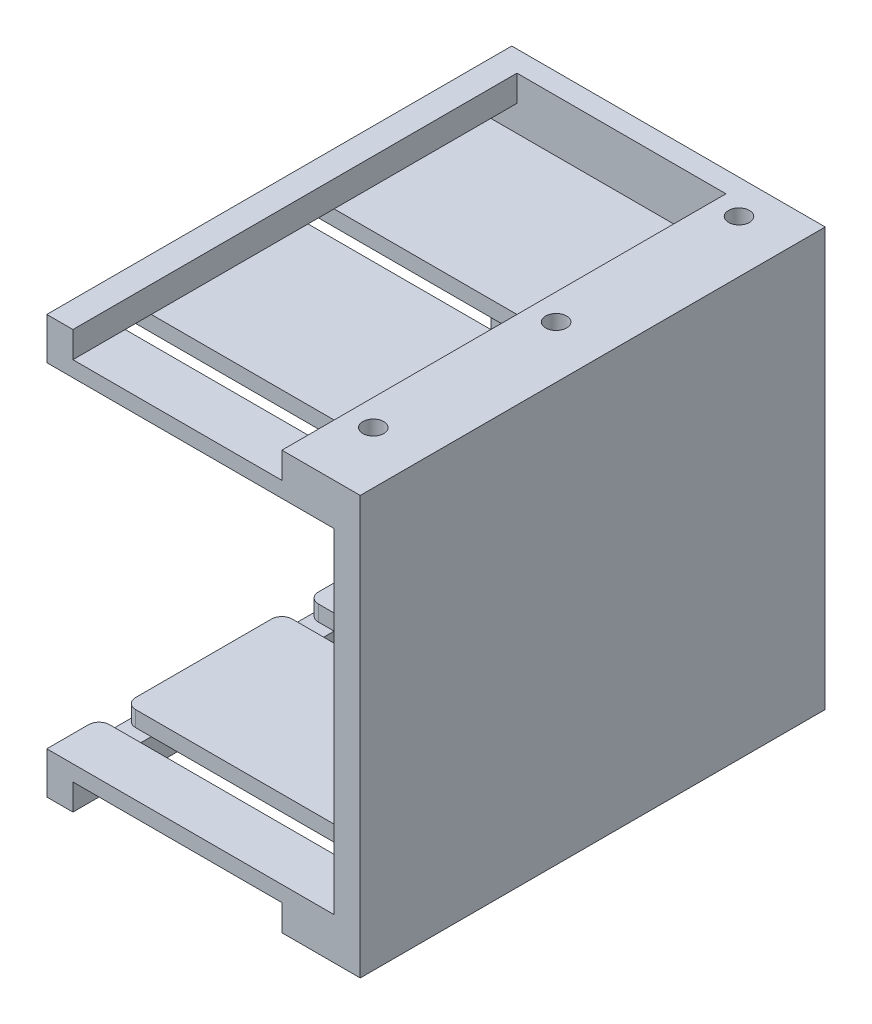
SolidWorks part; units mm, degrees
ref_plane "Front Plane" through (0, 0, 0) normal (1, 0, 0) x (0, 1, 0)
ref_plane "Top Plane" through (0, 0, 0) normal (0, 0, 1) x (0, 1, 0)
ref_plane "Right Plane" through (0, 0, 0) normal (0, 1, 0) x (-1, 0, 0)
sketch "Sketch1" plane through (0, 0, 0) normal (0, 0, 1) x (0, 1, 0)
  line L1 (0, 0) -> (-80, 0)
  line L2 (0, 0) -> (0, -60)
  line L3 (0, -60) -> (-80, -60)
  line L4 (-80, 0) -> (-80, -60)
  dimension "D1" = 80
  dimension "D2" = 60
extrude "Boss-Extrude1" add sketch "Sketch1" along normal blind 4
sketch "Sketch3" plane through (0, 0, 4) normal (0, 0, 1) x (1, 0, 0)
  line L0 (0, -40) -> (60, -40) construction
  line L1 (0, 0) -> (5, 0)
  line L2 (0, 0) -> (0, -5)
  line L3 (0, -5) -> (5, -5)
  line L4 (5, 0) -> (5, -5)
  line L5 (0, 0) -> (0, -80) construction
  line L6 (60, -80) -> (60, 0) construction
  line L7 (0, -75) -> (5, -75)
  line L8 (5, -80) -> (5, -75)
  line L9 (0, -80) -> (5, -80)
  line L10 (0, -80) -> (0, -75)
  line L16 (60, 0) -> (0, 0) construction
  line L17 (60, 0) -> (55, 0)
  line L18 (60, 0) -> (60, -80)
  line L19 (60, -80) -> (52.7053, -80)
  line L20 (55, -5) -> (55, -75)
  line L22 (55, -5) -> (45, -5)
  line L24 (55, 0) -> (45, 0)
  line L25 (45, -5) -> (45, 0)
  line L26 (52.7053, -80) -> (45, -80)
  line L28 (55, -75) -> (45, -75)
  line L29 (45, -80) -> (45, -75)
  dimension "D1" = 5
  dimension "D2" = 5
  dimension "D3" = 15
extrude "Boss-Extrude2" add sketch "Sketch3" along normal blind 85
sketch "Sketch9" plane through (55, 0, 0) normal (-1, 0, 0) x (0, -1, 0)
  line L0 (5, 89) -> (5, 4) construction
  line L1 (5, 9) -> (8, 9)
  line L2 (5, 9) -> (5, 39)
  line L3 (5, 39) -> (8, 39)
  line L4 (8, 9) -> (8, 39)
  line L5 (5, 89) -> (75, 89) construction
  line L6 (5, 44) -> (8, 44)
  line L7 (5, 44) -> (5, 74)
  line L8 (5, 74) -> (8, 74)
  line L9 (8, 44) -> (8, 74)
  line L10 (5, 79) -> (8, 79)
  line L11 (5, 79) -> (5, 89)
  line L12 (5, 89) -> (8, 89)
  line L13 (8, 79) -> (8, 89)
  line L14 (5, 4) -> (75, 4) construction
  line L15 (40, 89) -> (40, 4) construction
  line L16 (75, 39) -> (72, 39)
  line L17 (72, 9) -> (72, 39)
  line L18 (75, 9) -> (72, 9)
  line L19 (75, 9) -> (75, 39)
  line L20 (75, 74) -> (72, 74)
  line L21 (72, 44) -> (72, 74)
  line L22 (75, 44) -> (72, 44)
  line L23 (75, 44) -> (75, 74)
  line L24 (75, 89) -> (72, 89)
  line L25 (72, 79) -> (72, 89)
  line L26 (75, 79) -> (72, 79)
  line L27 (75, 79) -> (75, 89)
  dimension "D1" = 3
  dimension "D2" = 5
  dimension "D3" = 5
  dimension "D4" = 5
  dimension "D5" = 30
  dimension "D6" = 30
extrude "Boss-Extrude4" add sketch "Sketch9" along normal blind 55
fillet "Fillet2" radius 2 10 edges at (0, -73.5, 9) (0, -6.5, 9) (0, -6.5, 39) (0, -6.5, 44) (0, -73.5, 39) (0, -73.5, 44) (0, -73.5, 74) (0, -73.5, 79) (0, -6.5, 79) (0, -6.5, 74)
sketch "Sketch11" plane through (0, 0, 0) normal (0, 1, 0) x (-1, 0, 0)
  line L0 (-50, 89) -> (-50, 0) construction
  line L1 (-60, 89) -> (-45, 89) construction
  line L2 (-60, 0) -> (0, 0) construction
  line L3 (-45, 89) -> (-45, 4) construction
  line L4 (-25, 74) -> (-25, 79) construction
  line L5 (-5, 74) -> (-45, 74) construction
  line L6 (-5, 79) -> (-45, 79) construction
  line L7 (-25, 76.5) -> (-50, 76.5) construction
  line L8 (-25, 39) -> (-25, 44) construction
  line L9 (-5, 39) -> (-45, 39) construction
  line L10 (-5, 44) -> (-45, 44) construction
  line L11 (-25, 41.5) -> (-50, 41.5) construction
  line L12 (-25, 9) -> (-25, 4) construction
  line L13 (-5, 9) -> (-45, 9) construction
  line L14 (-45, 4) -> (-5, 4) construction
  line L15 (-25, 6.5) -> (-50, 6.5) construction
  circle A0 centre (-50, 76.5) radius 2
  circle A1 centre (-50, 41.5) radius 2
  circle A2 centre (-50, 6.5) radius 2
  dimension "D2" = 4
  dimension "D1" = 5
extrude "Cut-Extrude2" cut sketch "Sketch11" against normal blind 4.5
